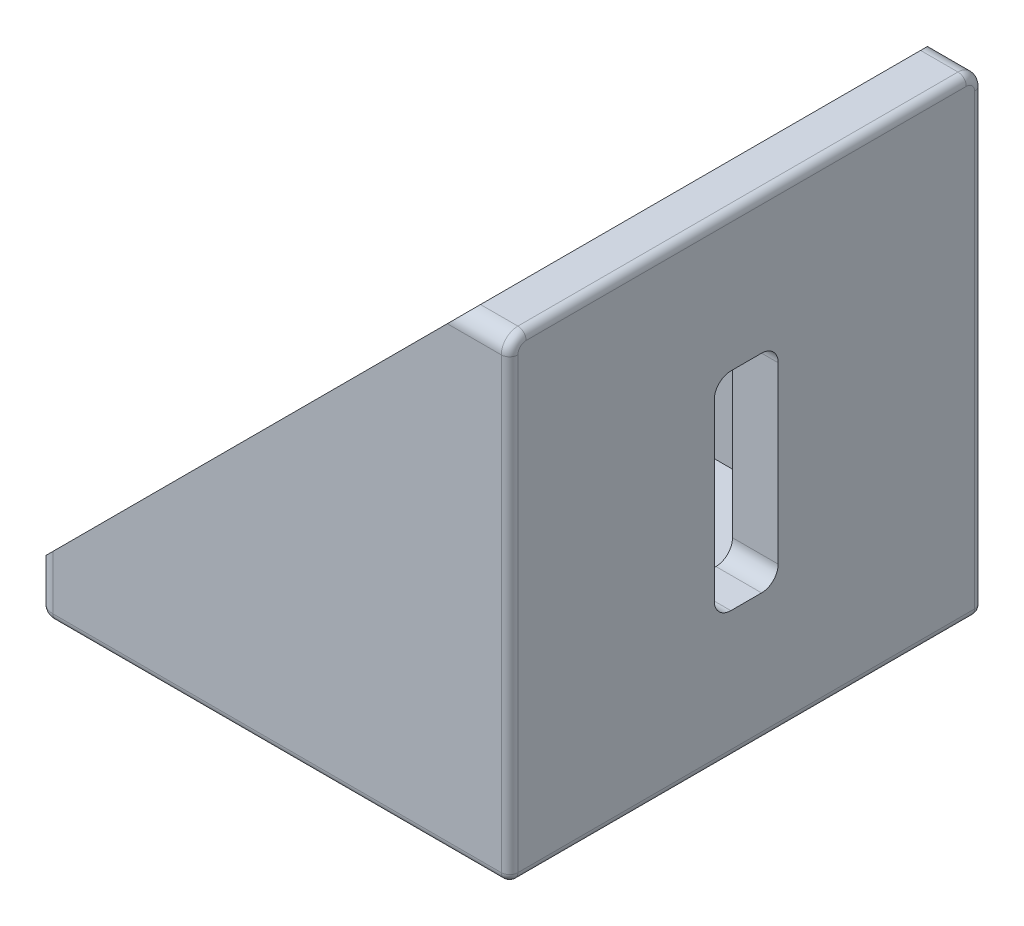
SolidWorks part; units mm, degrees
ref_plane "Front Plane" through (0, 0, 0) normal (0, 0, 1) x (1, 0, 0)
ref_plane "Top Plane" through (0, 0, 0) normal (0, 1, 0) x (1, 0, 0)
ref_plane "Right Plane" through (0, 0, 0) normal (1, 0, 0) x (0, 0, -1)
sketch "Sketch1" plane through (0, 0, 0) normal (0, 0, 1) x (1, 0, 0)
  line L0 (-57, 0) -> (0, 0)
  line L1 (0, 0) -> (0, 57)
  line L2 (0, 57) -> (-5.5, 57)
  line L3 (-5.5, 57) -> (-57, 5.5)
  line L4 (-57, 5.5) -> (-57, 0)
  dimension "D1" = 57
  dimension "D2" = 57
  dimension "D3" = 5.5
  dimension "D4" = 5.5
extrude "Boss-Extrude1" add sketch "Sketch1" along normal mid plane 57
sketch "Sketch2" plane through (0, 0, 0) normal (0, 0, 1) x (1, 0, 0)
  line L0 (-5.5, 57) -> (-5.5, 5.5)
  line L1 (-5.5, 5.5) -> (-57, 5.5)
  line L2 (-5.5, 57) -> (-57, 5.5)
extrude "Cut-Extrude1" cut sketch "Sketch2" against normal mid plane 46
sketch "Sketch3" plane through (-5.5, 0, 0) normal (-1, 0, 0) x (0, 0, 1)
  line L5 (-3.85, 15.5) -> (3.85, 15.5)
  line L6 (-3.85, 15.5) -> (-3.85, 40.5)
  line L11 (-3.85, 40.5) -> (3.85, 40.5)
  line L17 (3.85, 15.5) -> (3.85, 40.5)
  line L18 (-3.85, 15.5) -> (3.85, 40.5) construction
  line L23 (-3.85, 40.5) -> (3.85, 15.5) construction
  point P0 (0, 28)
  dimension "D1" = 25
  dimension "D2" = 7.7
  dimension "D3" = 28
extrude "Cut-Extrude2" cut sketch "Sketch3" against normal through all
sketch "Sketch4" plane through (0, 5.5, 0) normal (0, 1, 0) x (1, 0, 0)
  line L1 (-37.5, -3.85) -> (-12.5, -3.85)
  line L2 (-37.5, -3.85) -> (-37.5, 3.85)
  line L3 (-37.5, 3.85) -> (-12.5, 3.85)
  line L4 (-12.5, -3.85) -> (-12.5, 3.85)
  line L5 (-37.5, -3.85) -> (-12.5, 3.85) construction
  line L6 (-37.5, 3.85) -> (-12.5, -3.85) construction
  point P0 (-25, 0)
  dimension "D1" = 25
  dimension "D2" = 25
  dimension "D3" = 7.7
extrude "Cut-Extrude3" cut sketch "Sketch4" against normal through all
fillet "Fillet1" radius 2 4 edges at (-57, 2.75, -28.5) (-57, 2.75, 28.5) (-2.75, 57, -28.5) (-2.75, 57, 28.5)
fillet "Fillet2" radius 2 8 edges at (-37.5, 2.75, -3.85) (-37.5, 2.75, 3.85) (-12.5, 2.75, -3.85) (-12.5, 2.75, 3.85) (-2.75, 15.5, 3.85) (-2.75, 15.5, -3.85) (-2.75, 40.5, 3.85) (-2.75, 40.5, -3.85)
fillet "Fillet3" radius 1 11 edges at (-27.5, 0, 28.5) (-56.4142, 0, 27.9142) (-57, 0, 0) (-56.4142, 0, -27.9142) (0, 27.5, 28.5) (0, 56.4142, 27.9142) (0, 57, 0) (0, 56.4142, -27.9142) (0, 0, 0) (-27.5, 0, -28.5) (0, 27.5, -28.5)
